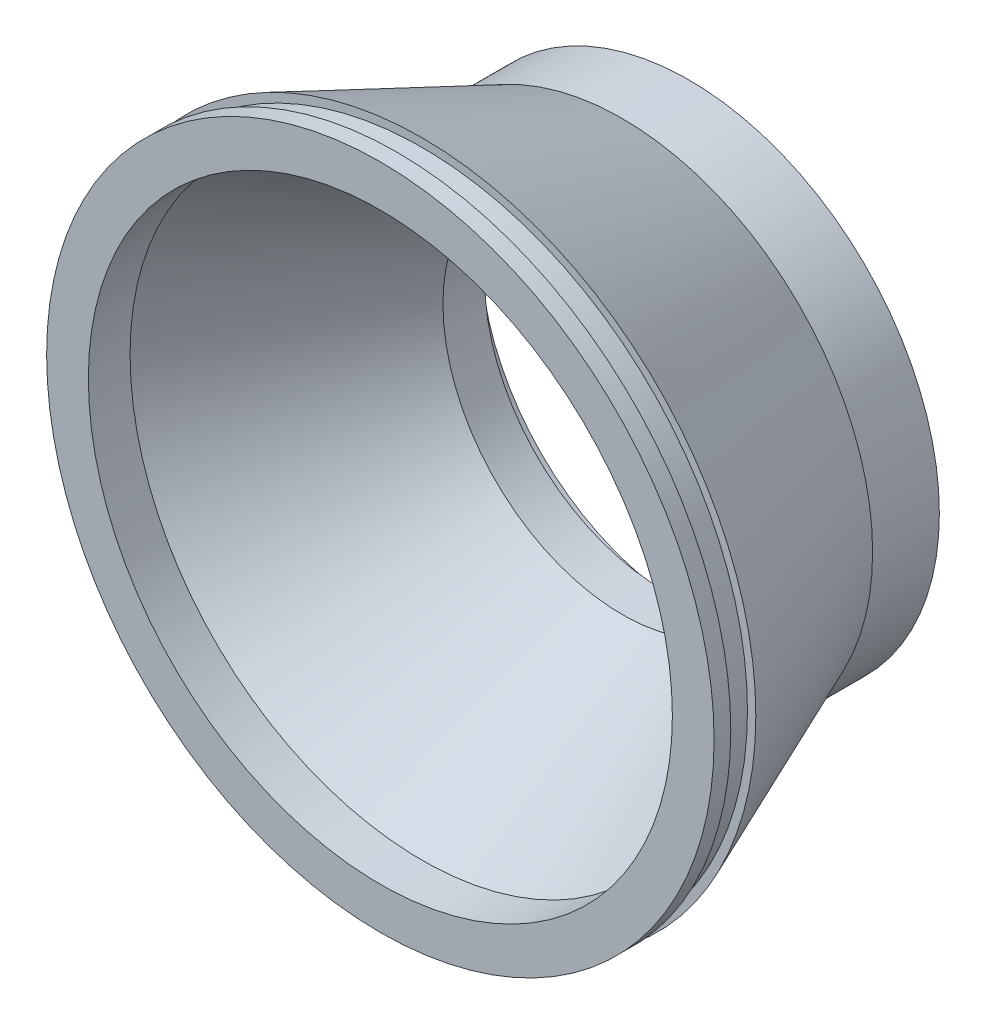
SolidWorks part; units mm, degrees
material "ABS"
ref_plane "Front Plane" through (0, 0, 0) normal (0, 0, 1) x (1, 0, 0)
ref_plane "Top Plane" through (0, 0, 0) normal (0, 1, 0) x (1, 0, 0)
ref_plane "Right Plane" through (0, 0, 0) normal (1, 0, 0) x (0, 0, -1)
sketch "Sketch2" plane through (0, 0, 0) normal (0, 0, 1) x (1, 0, 0)
  circle A0 centre (0, 0) radius 30
extrude "Boss-Extrude1" add sketch "Sketch2" along normal blind 8
sketch "Sketch3" plane through (0, 0, 0) normal (0, 0, -1) x (-1, 0, 0)
  circle A0 centre (0, 0) radius 21.5
extrude "Cut-Extrude1" cut sketch "Sketch3" against normal blind 8
sketch "Sketch4" plane through (0, 0, 0) normal (0, 0, -1) x (-1, 0, 0)
  circle A0 centre (0, 0) radius 25
extrude "Cut-Extrude2" cut sketch "Sketch4" against normal blind 3
sketch "Sketch5" plane through (0, 0, 0) normal (0, 0, -1) x (-1, 0, 0)
  line L0 (-24.82, 2.9946) -> (-25, 0)
  line L1 (-25, 0) -> (-24.82, -2.9946)
  line L2 (2.9946, 24.82) -> (0, 25)
  line L3 (0, 25) -> (-2.9946, 24.82)
  line L4 (24.82, -2.9946) -> (25, 0)
  line L5 (25, 0) -> (24.82, 2.9946)
  line L6 (2.9946, -24.82) -> (0, -25)
  line L7 (0, -25) -> (-2.9946, -24.82)
  circle A0 centre (0, 0) radius 25 construction
  arc A1 (2.9946, 24.82) -> (-2.9946, 24.82) centre (0, 25) ccw
  arc A2 (-24.82, 2.9946) -> (-24.82, -2.9946) centre (-25, 0) ccw
  arc A3 (-2.9946, -24.82) -> (2.9946, -24.82) centre (0, -25) ccw
  arc A4 (24.82, -2.9946) -> (24.82, 2.9946) centre (25, 0) ccw
extrude "Cut-Extrude3" cut sketch "Sketch5" against normal blind 3
sketch "Sketch8" plane through (0, 0, 3) normal (0, 0, -1) x (-1, 0, 0)
  arc A0 (-24.82, 2.9946) -> (-24.82, -2.9946) centre (0, 0) ccw
  arc A1 (2.9946, 24.82) -> (-2.9946, 24.82) centre (0, 25) ccw
  arc A2 (24.82, 2.9946) -> (24.82, -2.9946) centre (25, 0) cw
  arc A3 (-24.82, 2.9946) -> (-24.82, -2.9946) centre (-25, 0) ccw
  arc A4 (-2.9946, -24.82) -> (2.9946, -24.82) centre (0, -25) ccw
  arc A5 (2.9946, 24.82) -> (-2.9946, 24.82) centre (0, 0) ccw
  arc A6 (-2.9946, 24.82) -> (-24.82, 2.9946) centre (0, 0) ccw construction
  arc A7 (24.82, 2.9946) -> (24.82, -2.9946) centre (0, 0) cw
  arc A8 (-2.9946, -24.82) -> (2.9946, -24.82) centre (0, 0) ccw
  arc A9 (2.9946, -24.82) -> (24.82, -2.9946) centre (0, 0) ccw construction
sketch "Sketch12" plane through (0, 0, 3) normal (0, 0, -1) x (-1, 0, 0)
  arc A0 (-25, 0) -> (-21.6562, 12.4904) centre (0, 0) cw
  circle A2 centre (0, 0) radius 25 construction
sketch "Sketch19" plane through (0.0159, 0, 3) normal (0, 0, -1) x (-1, 0, 0)
  line L0 (-25, 0) -> (-27.5796, 1.5315)
  line L1 (-25, 0) -> (-28, 0)
  arc A0 (-27.5796, 1.5315) -> (-28, 0) centre (-25, 0) ccw
sketch "Sketch22" plane through (0, 0, 0) normal (0, 1, 0) x (1, 0, 0)
  line L0 (28, -3) -> (28, 0) construction
  line L1 (25, -3) -> (28, -3)
  line L2 (25, -3) -> (25, -0.5)
  line L3 (25, -0.5) -> (28, -0.5)
  line L4 (28, -3) -> (28, -0.5)
sketch "Sketch24" plane through (0, 0, 0) normal (0, 1, 0) x (1, 0, 0)
  line L1 (-25, -3) -> (-28, -3)
  line L2 (-25, -3) -> (-25, -0.5)
  line L3 (-25, -0.5) -> (-28, -0.5)
  line L4 (-28, -3) -> (-28, -0.5)
sketch3d "3DSketch1"
  line L1 (0, 25, 3) -> (0, 25, 0.5)
  line L2 (0, 25, 3) -> (0, 28, 3)
  line L3 (0, 28, 3) -> (0, 28, 0.5)
  line L4 (0, 25, 0.5) -> (0, 28, 0.5)
  line L5 (0, -25, 3) -> (0, -25, 0.5)
  line L6 (0, -25, 3) -> (0, -28, 3)
  line L7 (0, -28, 3) -> (0, -28, 0.5)
  line L8 (0, -25, 0.5) -> (0, -28, 0.5)
sweep "Cut-Sweep10" cut profiles "Sketch22" path "Sketch12"
sketch "Sketch30" plane through (0, 0, 3) normal (0, 0, -1) x (-1, 0, 0)
  arc A0 (0, -25) -> (-12.8017, -21.4736) centre (0, 0) cw
sweep "Cut-Sweep11" cut profiles "3DSketch1" path "Sketch30"
sketch "Sketch31" plane through (0, 0, 3) normal (0, 0, -1) x (-1, 0, 0)
  arc A0 (25, 0) -> (21.664, -12.4768) centre (0, 0) cw
sweep "Cut-Sweep12" cut profiles "Sketch24" path "Sketch31"
sketch "Sketch33" plane through (0, 0, 0) normal (0, 1, 0) x (1, 0, 0)
  line L5 (-21.5, -8) -> (-30, -8)
  line L7 (-40, -32) -> (-35, -32)
  line L8 (-40, -32) -> (-30, -8)
  line L9 (-21.5, -8) -> (-35, -32)
sketch "Sketch34" plane through (0, 0, 0) normal (0, 1, 0) x (1, 0, 0)
  line L0 (0, 0) -> (0, -29.2304)
revolve "Revolve1" add sketch "Sketch33" angle 360 about L0
sketch "Sketch36" plane through (0, 0, 32) normal (0, 0, 1) x (1, 0, 0)
  line L0 (-40, 0) -> (-39, 0)
  circle A0 centre (0, 0) radius 40 construction
sketch "Sketch37" plane through (0, 0, 0) normal (0, 1, 0) x (1, 0, 0)
  line L0 (-39, -32) -> (-39, -35)
  line L1 (-40, -32) -> (-39, -32) construction
  line L2 (-39, -35) -> (-40, -35)
  line L3 (-40, -35) -> (-40, -37)
  line L4 (-39, -32) -> (-35, -32)
  line L5 (-35, -32) -> (-35, -37)
  line L6 (-35, -37) -> (-40, -37)
revolve "Revolve2" add sketch "Sketch37" angle 360 about L0
